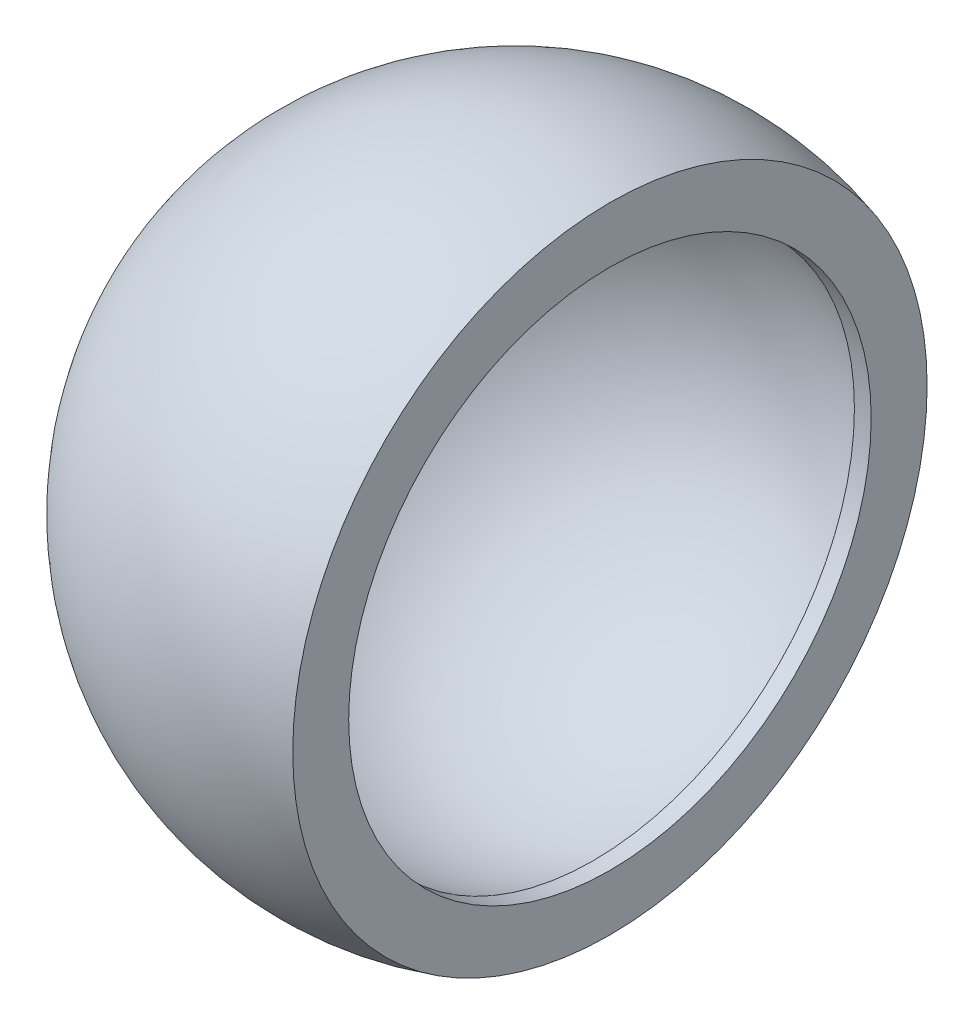
SolidWorks part; units mm, degrees
ref_plane "Alzado" through (0, 0, 0) normal (0, 0, 1) x (1, 0, 0)
ref_plane "Planta" through (0, 0, 0) normal (0, 1, 0) x (1, 0, 0)
ref_plane "Vista lateral" through (0, 0, 0) normal (1, 0, 0) x (0, 0, -1)
sketch "Croquis1" plane through (0, 0, 0) normal (0, 1, 0) x (1, 0, 0)
  line L0 (-10, 0) -> (-12.141, 0)
  line L2 (3.4828, 11.6308) -> (3.4828, 9.5797)
  line L3 (3.4828, 9.5797) -> (2.8686, 9.5797)
  arc A0 (2.8686, 9.5797) -> (-10, 0) centre (0, 0) ccw
  arc A1 (3.4828, 11.6308) -> (-12.141, 0) centre (0, 0) ccw
revolve "Revolución1" add sketch "Croquis1" angle 360 about L0
sketch3d "Croquis3D1"
  line L0 (2.8686, 0, 0) -> (3.4828, 0, 0) construction
  line L1 (3.4828, 11.6308, 0.0167) -> (3.4828, 12.2531, 0.0176)
  line L3 (3.4828, -0.027, 12.2531) -> (3.4828, 12.2308, 12.2754)
  line L4 (3.4828, 12.2531, 0.0176) -> (3.4828, 12.2308, 12.2754)
  line L5 (3.4828, -11.6308, -0.0138) -> (3.4828, -12.2531, -0.0146)
  line L6 (3.4828, -12.2476, -0.0146) -> (3.4828, -12.2622, 12.2262)
  line L7 (3.4828, -0.027, 12.2531) -> (3.4828, -12.2622, 12.2262)
  arc A0 (3.4828, -11.6308, -0.0138) -> (3.4828, 11.6308, 0.0167) centre (3.4828, 0, 0) ccw
  arc A1 (3.4828, -12.2531, -0.0146) -> (3.4828, -12.2481, 0.3518) centre (3.4828, 0, 0) ccw
  arc A2 (3.4828, 12.2531, 0.027) -> (3.4828, 12.2531, 0.0176) centre (3.4828, 0, 0) ccw
  point P1 (-8.7704, 0, 0)
  point P2 (-8.148, 0, 0)
  point P6 (-8.7704, 0, 0)
